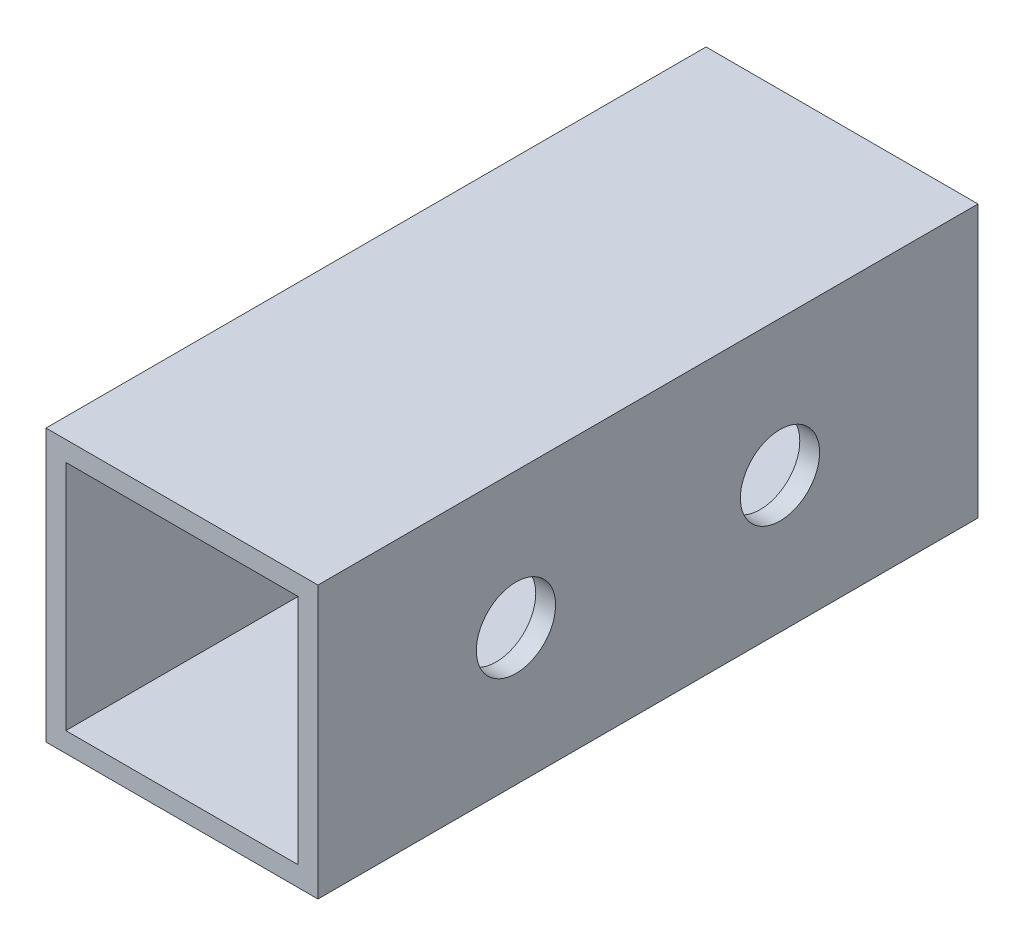
SolidWorks part; units mm, degrees
ref_plane "Спереди" through (0, 0, 0) normal (0, 0, 1) x (1, 0, 0)
ref_plane "Сверху" through (0, 0, 0) normal (0, 1, 0) x (1, 0, 0)
ref_plane "Справа" through (0, 0, 0) normal (1, 0, 0) x (0, 0, -1)
sketch "Эскиз1" plane through (0, 0, 0) normal (0, 0, 1) x (1, 0, 0)
  line L0 (-37.7868, 0.7437) -> (-20.1868, 0.7437)
  line L1 (-39.2868, 19.8437) -> (-18.6868, 19.8437)
  line L2 (-39.2868, 19.8437) -> (-39.2868, -0.7563)
  line L3 (-39.2868, -0.7563) -> (-18.6868, -0.7563)
  line L4 (-18.6868, 19.8437) -> (-18.6868, -0.7563)
  line L5 (-20.1868, 18.3437) -> (-20.1868, 0.7437)
  line L6 (-37.7868, 18.3437) -> (-20.1868, 18.3437)
  line L7 (-37.7868, 18.3437) -> (-37.7868, 0.7437)
  dimension "D1" = 20.6
  dimension "D2" = 20.6
  dimension "D3" = 1.5
extrude "Бобышка-Вытянуть1" add sketch "Эскиз1" along normal blind 50
sketch "Эскиз2" plane through (-18.6868, 0, 0) normal (1, 0, 0) x (0, 0, -1)
  line L0 (-50, 9.5437) -> (0, 9.5437) construction
  line L1 (-50, -0.7563) -> (-50, 19.8437) construction
  line L2 (0, -0.7563) -> (0, 19.8437) construction
  circle A0 centre (-35, 9.5437) radius 3
  circle A1 centre (-15, 9.5437) radius 3
  dimension "D1" = 15
  dimension "D2" = 15
extrude "Вырез-Вытянуть1" cut sketch "Эскиз2" against normal through all
